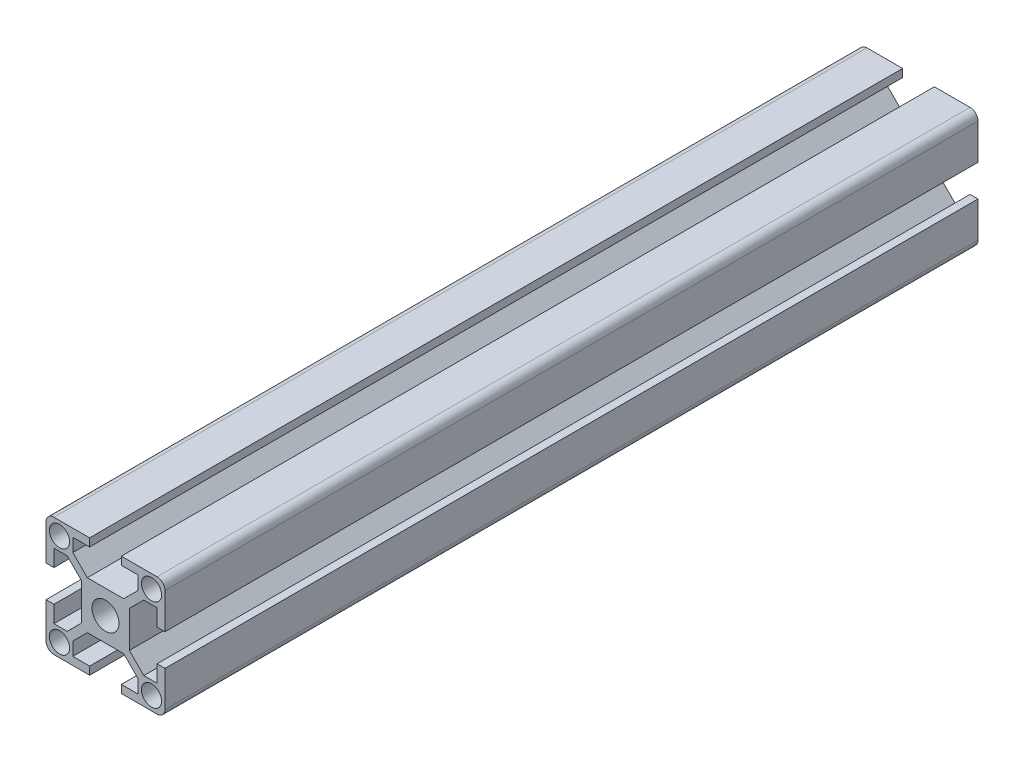
SolidWorks part; units mm, degrees
ref_plane "Front Plane" through (0, 0, 0) normal (0, 0, 1) x (1, 0, 0)
ref_plane "Top Plane" through (0, 0, 0) normal (0, 1, 0) x (1, 0, 0)
ref_plane "Right Plane" through (0, 0, 0) normal (1, 0, 0) x (0, 0, -1)
sketch "Sketch1" plane through (0, 0, 0) normal (0, 0, 1) x (1, 0, 0)
  line L0 (13, 4) -> (15, 4)
  line L1 (15, 4) -> (15, 13)
  line L2 (13, 15) -> (4, 15)
  line L3 (4, 15) -> (4, 13)
  line L4 (4, 13) -> (8.25, 13)
  line L5 (8.25, 13) -> (8.25, 9.6642)
  line L6 (8.25, 9.6642) -> (4.5858, 6)
  line L7 (4.5858, 6) -> (-4.5858, 6)
  line L8 (-4.5858, 6) -> (-8.25, 9.6642)
  line L9 (-8.25, 9.6642) -> (-8.25, 13)
  line L10 (-8.25, 13) -> (-4, 13)
  line L11 (-4, 13) -> (-4, 15)
  line L12 (-4, 15) -> (-13, 15)
  line L13 (-15, 13) -> (-15, 4)
  line L14 (-15, 4) -> (-13, 4)
  line L15 (-13, 4) -> (-13, 8.25)
  line L16 (-13, 8.25) -> (-9.6642, 8.25)
  line L17 (-9.6642, 8.25) -> (-6, 4.5858)
  line L18 (-6, 4.5858) -> (-6, -4.5858)
  line L19 (-6, -4.5858) -> (-9.6642, -8.25)
  line L20 (-9.6642, -8.25) -> (-13, -8.25)
  line L21 (-13, -8.25) -> (-13, -4)
  line L22 (-13, -4) -> (-15, -4)
  line L23 (-15, -4) -> (-15, -13)
  line L24 (-13, -15) -> (-4, -15)
  line L25 (-4, -15) -> (-4, -13)
  line L26 (-4, -13) -> (-8.25, -13)
  line L27 (-8.25, -13) -> (-8.25, -9.6642)
  line L28 (-8.25, -9.6642) -> (-4.5858, -6)
  line L29 (-4.5858, -6) -> (4.5858, -6)
  line L30 (4.5858, -6) -> (8.25, -9.6642)
  line L31 (8.25, -9.6642) -> (8.25, -13)
  line L32 (8.25, -13) -> (4, -13)
  line L33 (4, -13) -> (4, -15)
  line L34 (4, -15) -> (13, -15)
  line L35 (15, -13) -> (15, -4)
  line L36 (15, -4) -> (13, -4)
  line L37 (13, -4) -> (13, -8.25)
  line L38 (13, -8.25) -> (9.6642, -8.25)
  line L39 (9.6642, -8.25) -> (6, -4.5858)
  line L40 (6, -4.5858) -> (6, 4.5858)
  line L41 (6, 4.5858) -> (9.6642, 8.25)
  line L42 (9.6642, 8.25) -> (13, 8.25)
  line L43 (13, 8.25) -> (13, 4)
  circle A0 centre (-11.6, 11.6) radius 2.55
  circle A1 centre (11.6, -11.6) radius 2.55
  circle A2 centre (-11.6, -11.6) radius 2.55
  circle A3 centre (11.6, 11.6) radius 2.55
  circle A4 centre (0, 0) radius 3.4
  arc A5 (13, 15) -> (15, 13) centre (13, 13) cw
  arc A6 (-15, 13) -> (-13, 15) centre (-13, 13) cw
  arc A7 (-13, -15) -> (-15, -13) centre (-13, -13) cw
  arc A8 (15, -13) -> (13, -15) centre (13, -13) cw
  dimension "D1" = 5.1
  dimension "D2" = 6.8
  dimension "D3" = 2
  dimension "D8" = 2
  dimension "D9" = 4
  dimension "D4" = 11.6
  dimension "D5" = 11.6
  dimension "D6" = 11.6
  dimension "D7" = 11.6
  dimension "D10" = 4.5858
  dimension "D11" = 4.5858
  dimension "D12" = 6
  dimension "D13" = 8.25
  dimension "D14" = 9.6642
  dimension "D15" = 9.6642
  dimension "D16" = 15
  dimension "D17" = 4
  dimension "D18" = 4.5858
  dimension "D19" = 4.5858
  dimension "D20" = 6
  dimension "D21" = 8.25
  dimension "D22" = 9.6642
  dimension "D23" = 9.6642
  dimension "D24" = 4
  dimension "D25" = 4.5858
  dimension "D26" = 6
  dimension "D27" = 9.6642
extrude "Boss-Extrude1" add sketch "Sketch1" along normal blind 205
